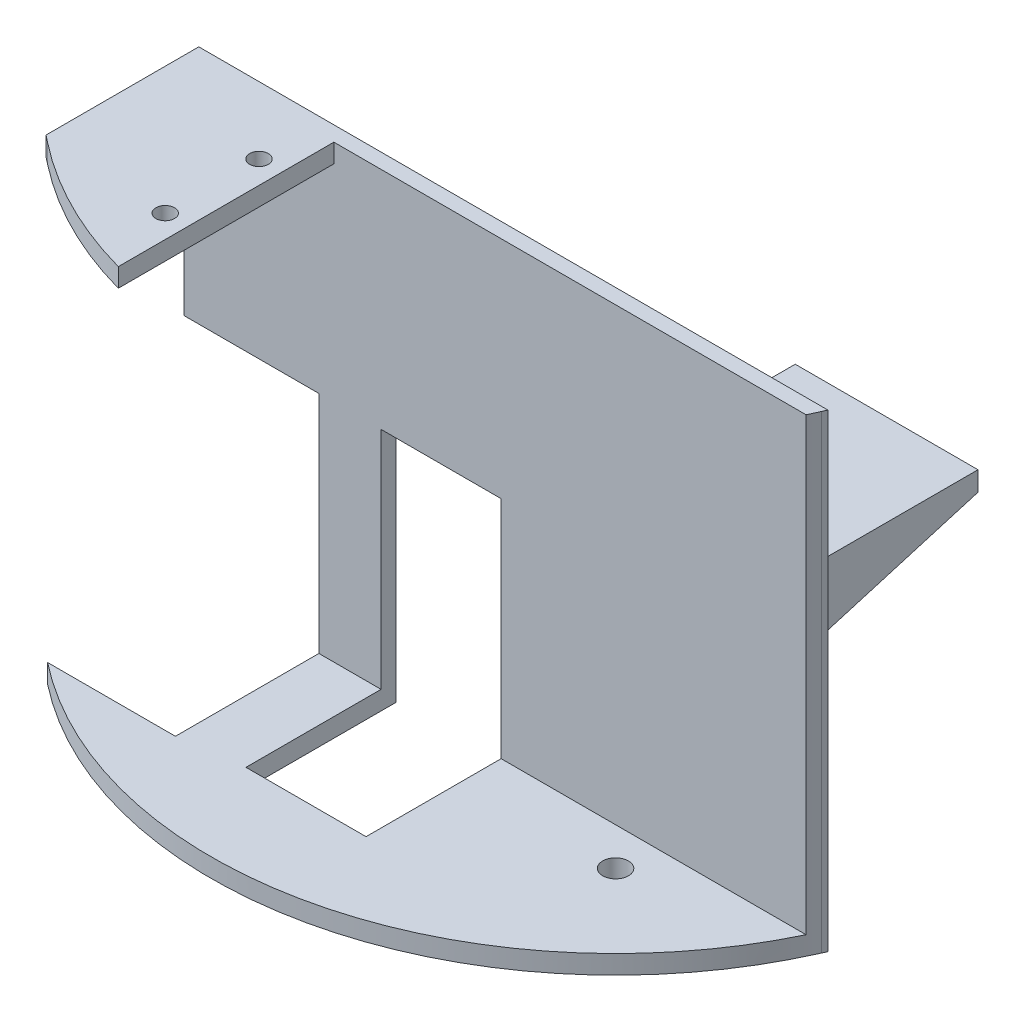
SolidWorks part; units mm, degrees
ref_plane "Front Plane" through (0, 0, 0) normal (0, 0, 1) x (1, 0, 0)
ref_plane "Top Plane" through (0, 0, 0) normal (0, 1, 0) x (1, 0, 0)
ref_plane "Right Plane" through (0, 0, 0) normal (1, 0, 0) x (0, 0, -1)
sketch "Sketch1" plane through (0, 0, 0) normal (0, 1, 0) x (1, 0, 0)
  circle A5 centre (-24.9914, 0) radius 2.1825
  circle A6 centre (46.8499, 0) radius 2.1825
  circle A7 centre (-24.9914, 0) radius 5.3575
  circle A8 centre (46.8499, 0) radius 5.3575
  dimension "D1" = 4.365
  dimension "D2" = 71.8414
  dimension "D3" = 3.175
extrude "Raiser" add sketch "Sketch1" along normal blind 4.7625
sketch "Sketch3" plane through (0, 4.7625, 0) normal (0, 1, 0) x (1, 0, 0)
  line L0 (-32.6114, 89.7259) -> (-32.6114, -17.8831) construction
  line L1 (-16.0583, 62.9089) -> (37.9167, 62.9089) construction
  line L2 (-16.0583, 62.9089) -> (-16.0583, 8.9339) construction
  line L3 (-16.0583, 8.9339) -> (37.9167, 8.9339) construction
  line L4 (37.9167, 62.9089) -> (37.9167, 8.9339) construction
  line L5 (-32.6114, 8.9339) -> (-32.6114, -17.8831)
  line L6 (-32.6114, 8.9339) -> (74.6661, 8.9339)
  line L7 (-31.8494, 8.1719) -> (73.5054, 8.1719) construction
  line L8 (-31.8494, 8.1719) -> (-31.8494, -17.5183) construction
  arc A0 (-32.6114, -17.8831) -> (74.6661, 8.9339) centre (10.9292, 35.9214) ccw
  circle A1 centre (-24.9914, 0) radius 2.1825 construction
  circle A2 centre (46.8499, 0) radius 2.1825 construction
  circle A3 centre (10.9292, 35.9214) radius 69.215 construction
  circle A4 centre (-24.9914, 0) radius 2.1825
  circle A5 centre (46.8499, 0) radius 2.1825
  arc A6 (-31.8494, -17.5183) -> (73.5054, 8.1719) centre (10.9292, 35.9214) ccw construction
  point P11 (-16.0583, 35.9214)
  point P13 (10.9292, 62.9089)
  dimension "D2" = 50.8
  dimension "D3" = 138.43
  dimension "D1" = 50.8
  dimension "D4" = 53.975
  dimension "D5" = 53.975
  dimension "D6" = 7.62
  dimension "D7" = 0.762
extrude "Platform" add sketch "Sketch3" along normal blind 3.175
sketch "Sketch7" plane through (0, 7.9375, 0) normal (0, 1, 0) x (1, 0, 0)
  line L0 (-32.6114, 8.9339) -> (74.6661, 8.9339)
  line L1 (73.5299, 6.3939) -> (-32.6114, 6.3939)
  line L4 (70.7095, 6.3939) -> (-30.0714, 6.3939) construction
  line L5 (74.6661, 8.9339) -> (-32.6114, 8.9339)
  line L6 (-32.6114, 8.9339) -> (-32.6114, -17.8831)
  line L7 (74.6661, 8.9339) -> (-32.6114, 8.9339)
  line L8 (-32.6114, 8.9339) -> (-32.6114, 6.3939)
  line L9 (-30.0714, 6.3939) -> (-30.0714, -16.6571) construction
  line L10 (-32.6114, 8.9339) -> (-32.6114, -17.8831) construction
  line L11 (-30.0714, 6.3939) -> (-30.0714, -19.843)
  line L12 (-32.6114, 8.9339) -> (-32.6114, -17.8831) construction
  arc A2 (-32.6114, -17.8831) -> (74.6661, 8.9339) centre (10.9292, 35.9214) ccw
  arc A3 (73.5299, 6.3939) -> (74.6661, 8.9339) centre (10.9292, 35.9214) ccw
  arc A4 (-30.0714, -16.6571) -> (70.7095, 6.3939) centre (10.9292, 35.9214) ccw construction
  arc A5 (-32.6114, -17.8831) -> (74.6661, 8.9339) centre (10.9292, 35.9214) ccw construction
  arc A6 (-32.6114, -17.8831) -> (74.6661, 8.9339) centre (10.9292, 35.9214) ccw construction
  arc A7 (-32.6114, -17.8831) -> (-30.0714, -19.843) centre (10.9292, 35.9214) ccw
  arc A8 (73.5299, 6.3939) -> (74.6661, 8.9339) centre (10.9292, 35.9214) ccw
  line M4 (74.6661, 8.9339) -> (-32.6114, 8.9339)
  line M5 (-32.6114, 8.9339) -> (-32.6114, -17.8831)
  arc M6 (-32.6114, -17.8831) -> (74.6661, 8.9339) centre (10.9292, 35.9214) ccw
  dimension "D3" = 2.54
  dimension "D1" = 0
  dimension "D2" = 2.54
extrude "Walls" add sketch "Sketch7" along normal blind 76.2 contours L1 M6 M4 M5
sketch "Sketch9" plane through (0, 0, -8.9339) normal (0, 0, -1) x (-1, 0, 0)
  line L0 (-74.6661, 62.6889) -> (-42.9161, 62.6889)
  line L1 (-74.6661, 84.1375) -> (-74.6661, 4.7625) construction
  line L2 (-42.9161, 62.6889) -> (-42.9161, 59.3869)
  line L3 (-42.9161, 59.3869) -> (-74.6661, 59.3869)
  line L4 (-74.6661, 59.3869) -> (-74.6661, 62.6889)
  dimension "D1" = 31.75
  dimension "D2" = 3.302
extrude "Boss-Extrude4" add sketch "Sketch9" along normal blind 25.4
sketch "Sketch10" plane through (42.9161, 0, 0) normal (-1, 0, 0) x (0, 0, 1)
  line L0 (-34.3339, 59.3869) -> (-8.9339, 51.8904)
  line L1 (-8.9339, 84.1375) -> (-8.9339, 4.7625) construction
  line L2 (-8.9339, 51.8904) -> (-8.9339, 59.3869)
  line L3 (-8.9339, 59.3869) -> (-34.3339, 59.3869)
extrude "Boss-Extrude5" add sketch "Sketch10" against normal blind 31.75
sketch "Sketch12" plane through (0, 84.1375, 0) normal (0, 1, 0) x (1, 0, 0)
  line L0 (-32.6114, 6.3939) -> (-32.6114, -17.8831)
  line L1 (-7.2114, 6.3939) -> (-7.2114, -30.8741)
  line L2 (73.5299, 6.3939) -> (-32.6114, 6.3939) construction
  line L3 (-32.6114, 6.3939) -> (-7.2114, 6.3939)
  arc A0 (-32.6114, -17.8831) -> (73.5299, 6.3939) centre (10.9292, 35.9214) ccw construction
  arc A1 (-32.6114, -17.8831) -> (-7.2114, -30.8741) centre (10.9292, 35.9214) ccw
  dimension "D1" = 25.4
extrude "Boss-Extrude6" add sketch "Sketch12" against normal blind 3.175
sketch "Sketch13" plane through (0, 84.1375, 0) normal (0, 1, 0) x (1, 0, 0)
  circle A0 centre (-11.0818, -2.4085) radius 1.5859
  circle A1 centre (-11.0818, -18.2835) radius 1.5859
  dimension "D1" = 15.875
extrude "Cut-Extrude1" cut sketch "Sketch13" against normal blind 3.175
sketch "Sketch14" plane through (0, 0, -6.3939) normal (0, 0, 1) x (1, 0, 0)
  line L1 (-32.6114, 7.9375) -> (-9.7514, 7.9375)
  line L2 (-32.6114, 7.9375) -> (-32.6114, 46.0375)
  line L3 (-32.6114, 46.0375) -> (-9.7514, 46.0375)
  line L4 (-9.7514, 7.9375) -> (-9.7514, 46.0375)
  dimension "D1" = 22.86
  dimension "D2" = 38.1
extrude "Cut-Extrude2" cut sketch "Sketch14" against normal blind 2.54
sketch "Sketch15" plane through (0, 7.9375, 0) normal (0, 1, 0) x (1, 0, 0)
  line L0 (-0.9191, 28.6299) -> (22.7776, 28.6299)
  line L1 (10.9292, 98.1361) -> (10.9292, -40.8763) construction
  line L2 (-32.6114, 8.9339) -> (-32.6114, -17.8831)
  line L3 (74.6661, 8.9339) -> (-32.6114, 8.9339)
  line L4 (-32.6114, 8.9339) -> (-32.6114, -17.8831)
  line L5 (74.6661, 8.9339) -> (-32.6114, 8.9339)
  arc A1 (-32.6114, -17.8831) -> (74.6661, 8.9339) centre (10.9292, 35.9214) ccw
  arc A2 (-32.6114, -17.8831) -> (74.6661, 8.9339) centre (10.9292, 35.9214) ccw
  circle A3 centre (46.8499, 0) radius 2.1825
  circle A4 centre (46.8499, 0) radius 2.1825
  circle A5 centre (-24.9914, 0) radius 2.1825
  circle A6 centre (-24.9914, 0) radius 2.1825
  point P2 (10.9292, 28.6299)
  point P16 (10.9292, 28.6299)
  dimension "D1" = 0
  dimension "D2" = 0
  dimension "D3" = 0
sketch "Sketch16" plane through (0, 7.9375, 0) normal (0, 1, 0) x (1, 0, 0)
  line L5 (-32.6114, 8.9339) -> (-9.7514, 8.9339)
  line L6 (-32.6114, 8.9339) -> (-32.6114, -17.8831)
  line L7 (-32.6114, -17.8831) -> (-9.7514, -17.8831)
  line L8 (-9.7514, 8.9339) -> (-9.7514, -17.8831)
  dimension "D1" = 22.86
extrude "Cut-Extrude3" cut sketch "Sketch16" against normal blind 5080
sketch "Sketch17" plane through (0, 0, -6.3939) normal (0, 0, 1) x (1, 0, 0)
  line L0 (74.6661, 7.9375) -> (-32.6114, 7.9375) construction
  line L1 (0.7692, 7.9375) -> (21.0892, 7.9375)
  line L2 (0.7692, 7.9375) -> (0.7692, 46.0375)
  line L3 (0.7692, 46.0375) -> (21.0892, 46.0375)
  line L4 (21.0892, 7.9375) -> (21.0892, 46.0375)
  point P6 (10.9292, 46.0375)
  dimension "D1" = 20.32
  dimension "D2" = 38.1
extrude "Cut-Extrude4" cut sketch "Sketch17" against normal blind 2.54
sketch "Sketch18" plane through (0, 7.9375, 0) normal (0, 1, 0) x (1, 0, 0)
  line L0 (21.0892, 8.9339) -> (21.0892, 6.3939) construction
  line L1 (0.7692, 8.9339) -> (21.0892, 8.9339)
  line L2 (0.7692, 8.9339) -> (0.7692, -16.4661)
  line L3 (0.7692, -16.4661) -> (21.0892, -16.4661)
  line L4 (21.0892, 8.9339) -> (21.0892, -16.4661)
  dimension "D1" = 25.4
  dimension "D2" = 0
extrude "Cut-Extrude5" cut sketch "Sketch18" against normal through all
sketch "Sketch21" plane through (0, 4.7625, 0) normal (0, -1, 0) x (1, 0, 0)
  circle A0 centre (35.6278, 7.1571) radius 23.435
extrude "Cut-Extrude6" cut sketch "Sketch21" along normal through all
sketch "Sketch22" plane through (0, 7.9375, 0) normal (0, 1, 0) x (1, 0, 0)
  line L0 (-31.8494, -17.5183) -> (-32.6114, -16.9083)
  line L1 (-32.6114, 8.9339) -> (-32.6114, -17.8831) construction
  line L2 (73.5054, 8.1719) -> (73.8433, 8.9339)
  line L3 (-32.6114, 8.9339) -> (74.6661, 8.9339) construction
  line L4 (73.8433, 8.9339) -> (74.6661, 8.9339)
  line L5 (-32.6114, -16.9083) -> (-32.6114, -17.8831)
  line L6 (-32.6114, -16.9083) -> (-32.6114, -17.8831)
  line L7 (-32.6114, -17.8831) -> (-31.3896, -17.8831)
  line L8 (-31.3896, -17.8831) -> (-32.6114, -16.9083)
  arc A1 (-31.8494, -17.5183) -> (73.5054, 8.1719) centre (10.9292, 35.9214) ccw construction
  arc A2 (-31.8494, -17.5183) -> (73.5054, 8.1719) centre (10.9292, 35.9214) ccw
  arc A3 (-32.6114, -17.8831) -> (74.6661, 8.9339) centre (10.9292, 35.9214) ccw
  line M4 (-9.7514, -17.8831) -> (-32.6114, -17.8831)
  arc M5 (-32.6114, -17.8831) -> (73.5299, 6.3939) centre (10.9292, 35.9214) ccw
  line M6 (73.5299, 6.3939) -> (21.0892, 6.3939)
extrude "Cut-Extrude7" cut sketch "Sketch22" against normal through all both and the other way through all contours A2 M4 M5 M6 | A3 L4 L2 A2 M6
sketch "Sketch23" plane through (0, 62.6889, 0) normal (0, 1, 0) x (1, 0, 0)
  line L0 (73.8433, 8.9339) -> (73.8433, 34.3339)
  line L1 (42.9161, 34.3339) -> (74.6661, 34.3339) construction
  line L2 (73.8433, 34.3339) -> (74.6661, 34.3339)
  line L3 (74.6661, 34.3339) -> (74.6661, 8.9339)
  line L4 (74.6661, 8.9339) -> (73.8433, 8.9339)
extrude "Cut-Extrude8" cut sketch "Sketch23" against normal through all both
sketch "Sketch24" plane through (0, 84.1375, 0) normal (0, 1, 0) x (1, 0, 0)
  line L0 (-32.6114, -17.8831) -> (-32.6114, -16.3077)
  line L1 (-32.6114, 8.9339) -> (-32.6114, -17.8831) construction
  line L2 (-32.6114, -17.8831) -> (-31.3896, -17.8831)
  line L3 (-31.3896, -17.8831) -> (-32.6114, -16.9222)
  arc A0 (-31.3896, -17.8831) -> (-7.2114, -30.0842) centre (10.9292, 35.9214) ccw construction
  line M8 (-32.6114, -17.8831) -> (-31.3896, -17.8831)
extrude "Cut-Extrude9" cut sketch "Sketch24" against normal through all both contours L3 L0 M8
